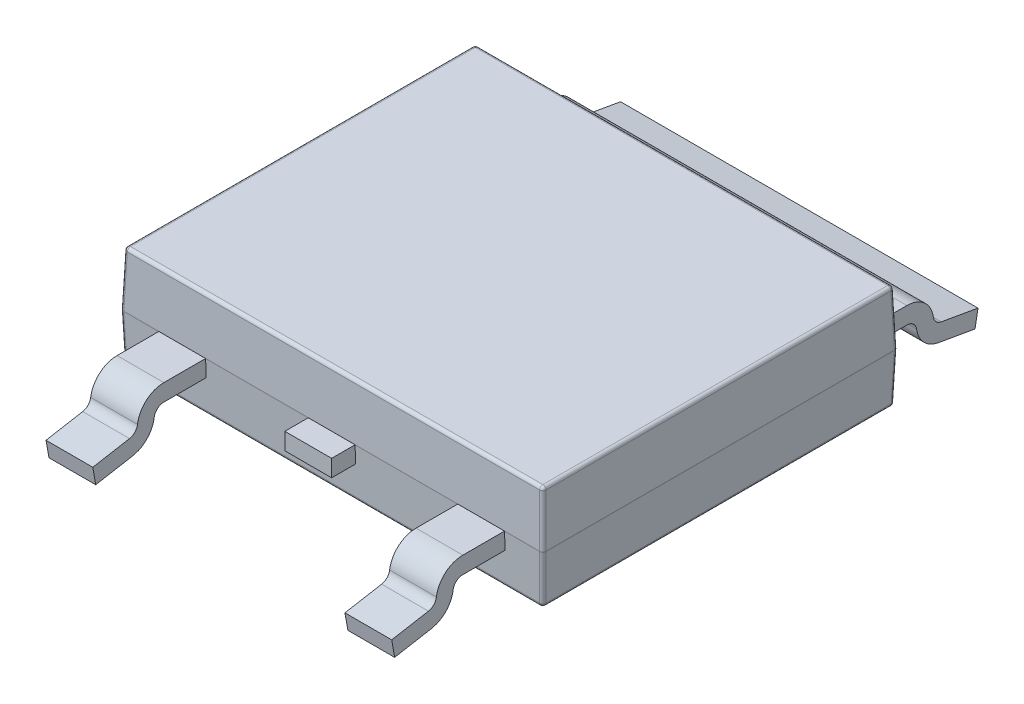
SolidWorks part; units mm, degrees
ref_plane "Front" through (0, 0, 0) normal (0, 0, 1) x (1, 0, 0)
ref_plane "Top" through (0, 0, 0) normal (0, 1, 0) x (1, 0, 0)
ref_plane "Right" through (0, 0, 0) normal (1, 0, 0) x (0, 0, -1)
sketch "Sketch1" plane through (0, 0, 0) normal (0, 1, 0) x (1, 0, 0)
  line L0 (0, 2.73) -> (0, -2.73) construction
  line L1 (-3.25, 2.73) -> (3.25, 2.73)
  line L2 (-3.25, 2.73) -> (-3.25, -2.73)
  line L3 (-3.25, -2.73) -> (3.25, -2.73)
  line L4 (3.25, 2.73) -> (3.25, -2.73)
  dimension "D1" = 5.46
  dimension "D2" = 6.5
extrude "Extrude1" add sketch "Sketch1" along normal blind 0.8375 draft 2 and the other way blind 0.7625 draft 2
fillet "Fillet1" radius 0.05 20 edges at (3.2208, 0.8375, 0) (-3.2234, -0.7625, 0) (-3.2367, -0.3813, 2.7167) (0, -0.7625, -2.7034) (0, 0.8375, -2.7008) (-3.2367, -0.3813, -2.7167) (3.2234, -0.7625, 0) (3.2367, -0.3813, -2.7167) (0, -0.7625, 2.7034) (3.2367, -0.3813, 2.7167) (-3.2208, 0.8375, 0) (0, 0, -2.73) (3.25, 0, 0) (0, 0, 2.73) (-3.25, 0, 0) (0, 0.8375, 2.7008) (-3.2354, 0.4188, -2.7154) (3.2354, 0.4188, -2.7154) (3.2354, 0.4188, 2.7154) (-3.2354, 0.4188, 2.7154)
sketch "Sketch2" plane through (0, 0, 0) normal (1, 0, 0) x (0, 0, -1)
  line L0 (0, 0) -> (0, -0.26)
  line L1 (0, 0) -> (-3.3723, 0)
  line L2 (-2.7209, 0) -> (-2.7209, -0.26) construction
  line L3 (0, -0.26) -> (-3.3723, -0.26)
  line L4 (-3.8559, -0.7379) -> (-4.4209, -0.8375)
  line L5 (-4.4209, -0.8375) -> (-4.4661, -0.5814)
  line L6 (-4.4661, -0.5814) -> (-3.9011, -0.4818)
  line L8 (-2.6754, -1.5625) -> (-2.7034, -0.7625) construction
  line L10 (-2.7592, 0.8375) -> (2.7592, 0.8375) construction
  line L11 (-2.7034, -0.7625) -> (2.7034, -0.7625) construction
  arc A0 (-3.9011, -0.4818) -> (-3.7785, -0.3544) centre (-3.9271, -0.3341) ccw
  arc A1 (-3.3723, -0.26) -> (-3.5209, -0.3897) centre (-3.3723, -0.41) ccw
  arc A2 (-3.3723, 0) -> (-3.7785, -0.3544) centre (-3.3723, -0.41) ccw
  arc A3 (-3.8559, -0.7379) -> (-3.5209, -0.3897) centre (-3.9271, -0.3341) ccw
  dimension "D2" = 0.15
  dimension "D3" = 0.9
  dimension "D1" = 0.26
  dimension "D4" = 1.7
  dimension "D5" = 1.675
  dimension "D6" = 10
extrude "Extrude2" add sketch "Sketch2" along normal mid plane 0.72
pattern_linear "LPattern3" count 2 spacing 2.3 along (-1, 0, 0) count 2 spacing 2.3 along (1, 0, 0) of "Extrude2"
sketch "Sketch3" plane through (0, 0, 0) normal (1, 0, 0) x (0, 0, -1)
  line L0 (4.4209, -0.8375) -> (3.8559, -0.7379)
  line L1 (4.4661, -0.5814) -> (4.4209, -0.8375)
  line L2 (3.9011, -0.4818) -> (4.4661, -0.5814)
  line L6 (-3.3723, -0.26) -> (0, -0.26)
  line L7 (0, -0.26) -> (0, 0)
  line L8 (0, 0) -> (-3.3723, 0)
  line L9 (-3.9011, -0.4818) -> (-4.4661, -0.5814)
  line L10 (-4.4661, -0.5814) -> (-4.4209, -0.8375)
  line L11 (-4.4209, -0.8375) -> (-3.8559, -0.7379)
  line L12 (0, -0.26) -> (3.3723, -0.26)
  line L13 (0, -0.26) -> (0, 0)
  line L14 (3.3723, 0) -> (0, 0)
  arc A0 (3.8559, -0.7379) -> (3.5209, -0.3897) centre (3.9271, -0.3341) cw
  arc A1 (3.9011, -0.4818) -> (3.7785, -0.3544) centre (3.9271, -0.3341) cw
  arc A2 (3.3723, 0) -> (3.7785, -0.3544) centre (3.3723, -0.41) cw
  arc A3 (3.3723, -0.26) -> (3.5209, -0.3897) centre (3.3723, -0.41) cw
  arc A4 (-3.3723, -0.26) -> (-3.5209, -0.3897) centre (-3.3723, -0.41) ccw
  arc A5 (-3.3723, 0) -> (-3.7785, -0.3544) centre (-3.3723, -0.41) ccw
  arc A6 (-3.9011, -0.4818) -> (-3.7785, -0.3544) centre (-3.9271, -0.3341) ccw
  arc A7 (-3.8559, -0.7379) -> (-3.5209, -0.3897) centre (-3.9271, -0.3341) ccw
  dimension "D1" = 0
extrude "Extrude3" add sketch "Sketch3" along normal mid plane 5.5
ref_plane "Contact Plane" through (0, -0.8375, 0) normal (0, 1, 0) x (-1, 0, 0)
sketch "Sketch - Land Pattern" plane through (0, -0.8375, 0) normal (0, 1, 0) x (-1, 0, 0)
  line L0 (2.8, 3.15) -> (1.8, 3.15) construction
  line L1 (-1.65, -2.4) -> (1.65, -2.4)
  line L2 (-1.65, -2.4) -> (-1.65, -3.9)
  line L3 (-1.65, -3.9) -> (1.65, -3.9)
  line L4 (1.65, -2.4) -> (1.65, -3.9)
  line L5 (1.8, 3.9) -> (2.8, 3.9)
  line L6 (1.8, 3.9) -> (1.8, 2.4)
  line L7 (1.8, 2.4) -> (2.8, 2.4)
  line L8 (2.8, 3.9) -> (2.8, 2.4)
  line L9 (2.3, 3.9) -> (2.3, 2.4) construction
  line L10 (0, -2.4) -> (0, -3.9) construction
  line L11 (-1.65, -3.15) -> (1.65, -3.15) construction
  line L12 (0, 0) -> (2.8, 0) construction
  line L13 (0.5, 3.9) -> (0.5, 2.4)
  line L14 (-0.5, 2.4) -> (0.5, 2.4)
  line L15 (-0.5, 3.9) -> (-0.5, 2.4)
  line L16 (-0.5, 3.9) -> (0.5, 3.9)
  line L17 (-1.8, 3.9) -> (-1.8, 2.4)
  line L18 (-2.8, 2.4) -> (-1.8, 2.4)
  line L19 (-2.8, 3.9) -> (-2.8, 2.4)
  line L20 (-2.8, 3.9) -> (-1.8, 3.9)
  line L21 (2.8, 3.9) -> (0.5, 3.9) construction
  dimension "D1" = 3.3
  dimension "D2" = 1.5
  dimension "D3" = 6.3
  dimension "D4" = 2.3
  dimension "D5" = 1
  dimension "D6" = 2.3
sketch "Esboço1" plane through (0, 0, 0) normal (0, 1, 0) x (1, 0, 0)
  line L1 (-0.7894, -3.0907) -> (0.7775, -3.0907)
  line L2 (-0.7894, -3.0907) -> (-0.7894, -4.851)
  line L3 (-0.7894, -4.851) -> (0.7775, -4.851)
  line L4 (0.7775, -3.0907) -> (0.7775, -4.851)
extrude "Corte-extrusão1" cut sketch "Esboço1" against normal blind 10
